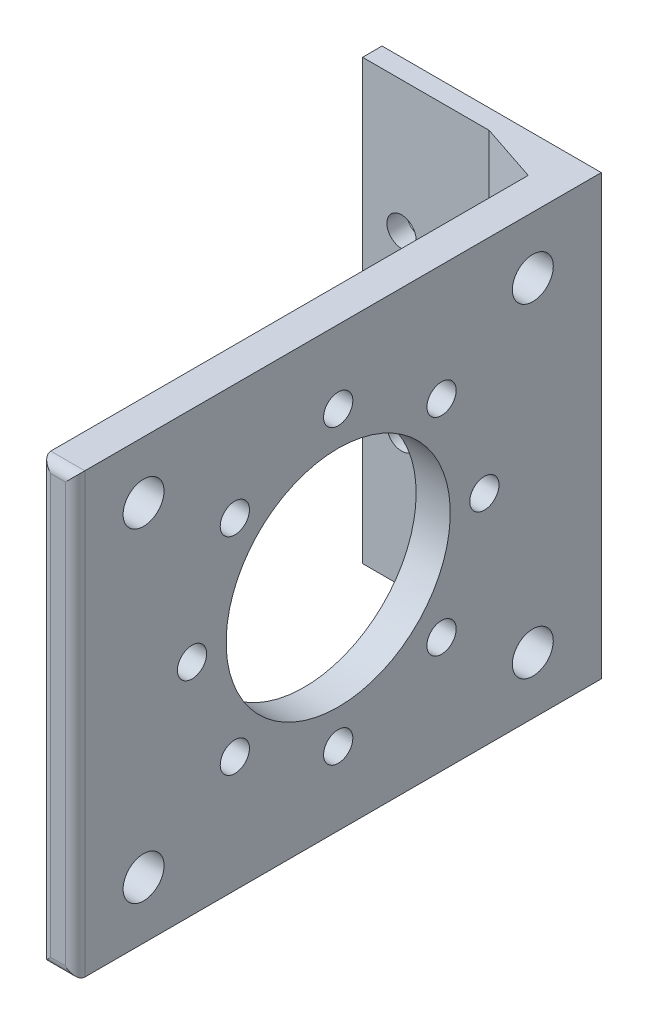
SolidWorks part; units mm, degrees
ref_plane "前视基准面" through (0, 0, 0) normal (0, 0, 1) x (1, 0, 0)
ref_plane "上视基准面" through (0, 0, 0) normal (0, 1, 0) x (1, 0, 0)
ref_plane "右视基准面" through (0, 0, 0) normal (1, 0, 0) x (0, 0, -1)
sketch "草图1" plane through (0, 0, 0) normal (0, 0, 1) x (1, 0, 0)
  line L1 (0, 0) -> (22.5, 0)
  line L2 (0, 0) -> (0, -45)
  line L3 (0, -45) -> (22.5, -45)
  line L4 (22.5, 0) -> (22.5, -45)
  dimension "D1" = 45
  dimension "D2" = 22.5
extrude "凸台-拉伸1" add sketch "草图1" along normal blind 2
sketch "草图2" plane through (0, 0, 2) normal (0, 0, 1) x (1, 0, 0)
  line L0 (22.5, 0) -> (22.5, -45)
  line L1 (22.5, -45) -> (19, -45)
  line L2 (0, -45) -> (22.5, -45) construction
  line L3 (19, -45) -> (19, 0)
  line L4 (22.5, 0) -> (0, 0) construction
  line L5 (19, 0) -> (22.5, 0)
  dimension "D1" = 3.5
extrude "凸台-拉伸2" add sketch "草图2" along normal blind 52
sketch "草图3" plane through (22.5, 0, 0) normal (1, 0, 0) x (0, 0, -1)
  line L0 (-54, 0) -> (0, -45) construction
  line L2 (-27, -22.5) -> (-54, -22.5) construction
  line L3 (-54, -45) -> (-54, 0) construction
  circle A0 centre (-27, -22.5) radius 21.25 construction
  circle A1 centre (-27, -22.5) radius 26 construction
  circle A2 centre (-46.9738, -5.8552) radius 2.1
  circle A3 centre (-7.0262, -39.1448) radius 2.1
  circle A4 centre (-27, -22.5) radius 32.5 construction
  arc A5 (-51.9672, -1.694) -> (-43.6261, -35.7339) centre (-17.9367, -11.3971) ccw construction
  arc A6 (-51.9672, -1.694) -> (-16.9812, -3.76) centre (-36.2865, -33.4169) cw construction
  arc A7 (-2.0328, -43.306) -> (-12.4518, -7.0109) centre (-36.8737, -33.6645) ccw construction
  arc A8 (-2.0328, -43.306) -> (-39.6117, -39.6028) centre (-17.799, -10.7749) cw construction
  circle A9 centre (-27, -22.5) radius 11.5
  circle A10 centre (-46.9738, -39.1448) radius 2.1
  circle A11 centre (-7.0262, -5.8552) radius 2.1
  circle A12 centre (-27, -22.5) radius 15 construction
  circle A13 centre (-42, -22.5) radius 1.5
  circle A17 centre (-37.6066, -11.8934) radius 1.5
  circle A18 centre (-27, -7.5) radius 1.5
  circle A19 centre (-16.3934, -11.8934) radius 1.5
  circle A20 centre (-12, -22.5) radius 1.5
  circle A21 centre (-16.3934, -33.1066) radius 1.5
  circle A22 centre (-27, -37.5) radius 1.5
  circle A23 centre (-37.6066, -33.1066) radius 1.5
  point P49 (-27, -22.5)
  dimension "D1" = 42.5
  dimension "D2" = 52
  dimension "D3" = 4.2
  dimension "D4" = 65
  dimension "D5" = 23
  dimension "D6" = 30
  dimension "D7" = 3
  dimension "D8" = 8
extrude "切除-拉伸2" cut sketch "草图3" against normal up to next
chamfer "倒角1" distance 6 distance2 2 1 edges at (19, -22.5, 2)
fillet "圆角1" radius 1 4 edges at (22.5, -22.5, 54) (20.75, -45, 54) (19, -22.5, 54) (20.75, 0, 54)
sketch "草图4" plane through (0, 0, 2) normal (0, 0, 1) x (1, 0, 0)
  line L0 (0, 0) -> (0, -45) construction
  line L1 (0, -45) -> (13, -45) construction
  line L2 (0, -22.5) -> (13, -22.5) construction
  line L3 (13, -45) -> (13, 0) construction
  line L4 (0, -45) -> (10, -45) construction
  line L5 (10, -45) -> (10, 0) construction
  line L6 (13, 0) -> (0, 0) construction
  circle A0 centre (4, -31.5) radius 1.5
  circle A2 centre (4, -13.5) radius 1.5
  circle A3 centre (16, -13.5) radius 1.5
  circle A4 centre (16, -31.5) radius 1.5
  dimension "D3" = 3
  dimension "D1" = 4
  dimension "D2" = 13.5
  dimension "D4" = 10
extrude "切除-拉伸3" cut sketch "草图4" against normal mid plane 10
sketch "草图5" plane through (0, 0, 2) normal (0, 0, 1) x (1, 0, 0)
  circle A0 centre (16, -13.5) radius 2.2471
  circle A1 centre (16, -31.5) radius 2.2471
extrude "切除-拉伸4" cut sketch "草图5" against normal blind 0.001 and the other way blind 15
